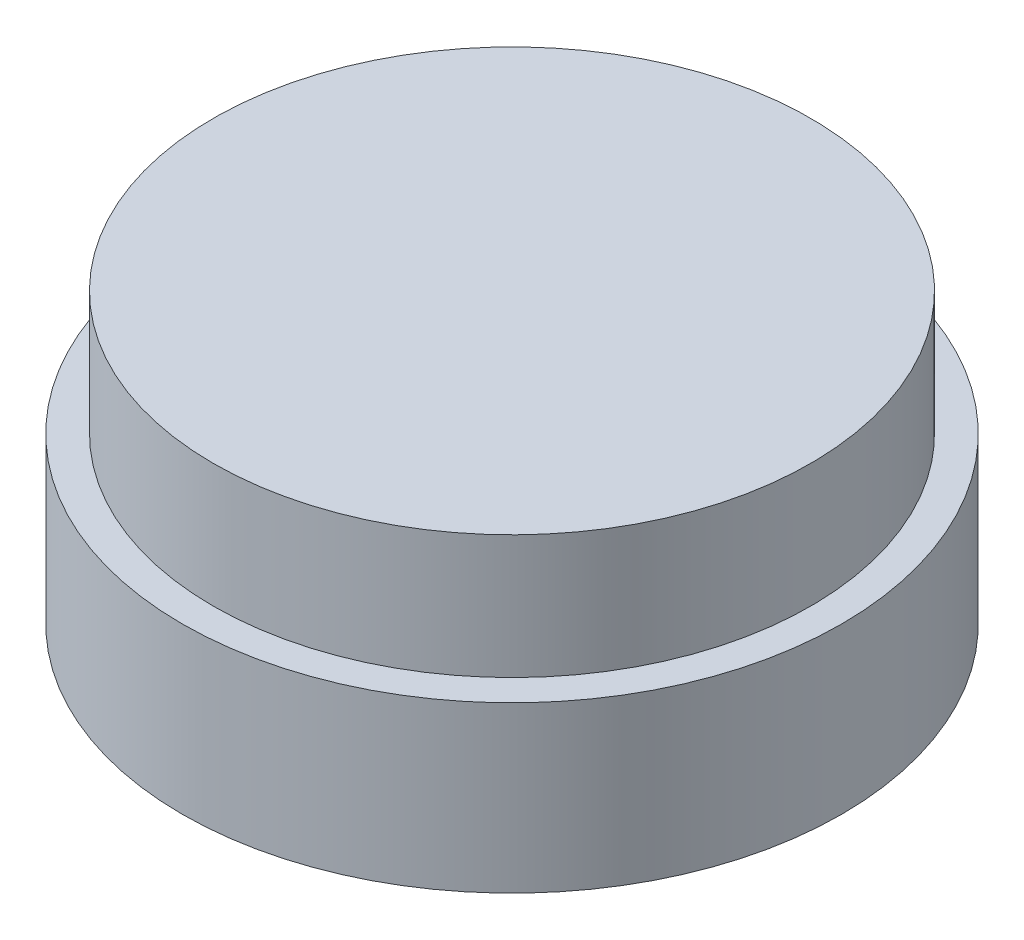
SolidWorks part; units mm, degrees
ref_plane "Płaszczyzna przednia" through (0, 0, 0) normal (0, 0, 1) x (1, 0, 0)
ref_plane "Płaszczyzna górna" through (0, 0, 0) normal (0, 1, 0) x (1, 0, 0)
ref_plane "Płaszczyzna prawa" through (0, 0, 0) normal (1, 0, 0) x (0, 0, -1)
sketch "Szkic1" plane through (0, 0, 0) normal (0, 1, 0) x (1, 0, 0)
  circle A0 centre (0, 0) radius 8
  dimension "D1" = 16
extrude "Dodanie-wyciągnięcie2" add sketch "Szkic1" along normal blind 4
sketch "Szkic2" plane through (0, 4, 0) normal (0, 1, 0) x (1, 0, 0)
  circle A0 centre (0, 0) radius 7.25
  dimension "D1" = 14.5
extrude "Dodanie-wyciągnięcie4" add sketch "Szkic2" along normal blind 3
